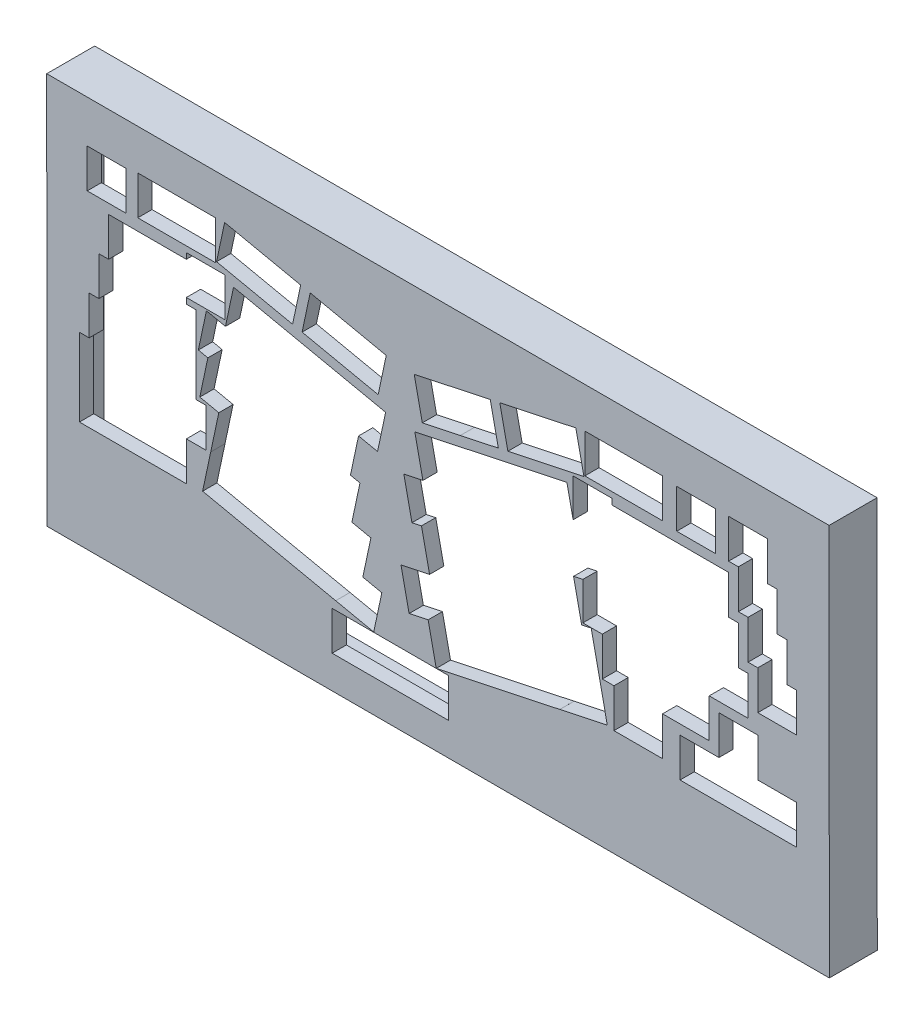
SolidWorks part; units mm, degrees
ref_plane "Front Plane" through (0, 0, 0) normal (0, 0, 1) x (1, 0, 0)
ref_plane "Top Plane" through (0, 0, 0) normal (0, 1, 0) x (1, 0, 0)
ref_plane "Right Plane" through (0, 0, 0) normal (1, 0, 0) x (0, 0, -1)
sketch "Model" plane through (0, 0, 0) normal (0, 0, 1) x (1, 0, 0)
  line L0 (3.8158, 5.1291) -> (3.565, 5.0023) construction
  line L1 (3.565, 5.0023) -> (3.3652, 4.8038) construction
  line L2 (3.3652, 4.8038) -> (3.2384, 4.5531) construction
  line L3 (3.2384, 4.5531) -> (3.1943, 4.2733) construction
  line L4 (3.1943, 4.2733) -> (3.2384, 3.9949) construction
  line L5 (3.2384, 3.9949) -> (3.3652, 3.7441) construction
  line L6 (3.3652, 3.7441) -> (3.565, 3.5457) construction
  line L7 (3.565, 3.5457) -> (3.8158, 3.4189) construction
  line L8 (3.8158, 3.4189) -> (4.0942, 3.3734) construction
  line L9 (4.0942, 3.3734) -> (4.3725, 3.4189) construction
  line L10 (4.3725, 3.4189) -> (4.6233, 3.5457) construction
  line L11 (4.6233, 3.5457) -> (4.8231, 3.7441) construction
  line L12 (4.8231, 3.7441) -> (4.9499, 3.9949) construction
  line L13 (4.9499, 3.9949) -> (4.994, 4.2733) construction
  line L14 (4.994, 4.2733) -> (4.9499, 4.5531) construction
  line L15 (4.9499, 4.5531) -> (4.8231, 4.8038) construction
  line L16 (4.8231, 4.8038) -> (4.6233, 5.0023) construction
  line L17 (4.6233, 5.0023) -> (4.3725, 5.1291) construction
  line L18 (4.3725, 5.1291) -> (4.0942, 5.1732) construction
  line L19 (4.0942, 5.1732) -> (3.8158, 5.1291) construction
  line L20 (75.7107, 5.1291) -> (75.4599, 5.0023) construction
  line L21 (75.4599, 5.0023) -> (75.2602, 4.8038) construction
  line L22 (75.2602, 4.8038) -> (75.1321, 4.5531) construction
  line L23 (75.1321, 4.5531) -> (75.088, 4.2733) construction
  line L24 (75.088, 4.2733) -> (75.1321, 3.9949) construction
  line L25 (75.1321, 3.9949) -> (75.2602, 3.7441) construction
  line L26 (75.2602, 3.7441) -> (75.4599, 3.5457) construction
  line L27 (75.4599, 3.5457) -> (75.7107, 3.4189) construction
  line L28 (75.7107, 3.4189) -> (75.989, 3.3734) construction
  line L29 (75.989, 3.3734) -> (76.2663, 3.4189) construction
  line L30 (76.2663, 3.4189) -> (76.5168, 3.5457) construction
  line L31 (76.5168, 3.5457) -> (76.7168, 3.7441) construction
  line L32 (76.7168, 3.7441) -> (76.8449, 3.9949) construction
  line L33 (76.8449, 3.9949) -> (76.889, 4.2733) construction
  line L34 (76.889, 4.2733) -> (76.8449, 4.5531) construction
  line L35 (76.8449, 4.5531) -> (76.7168, 4.8038) construction
  line L36 (76.7168, 4.8038) -> (76.5168, 5.0023) construction
  line L37 (76.5168, 5.0023) -> (76.2663, 5.1291) construction
  line L38 (76.2663, 5.1291) -> (75.989, 5.1732) construction
  line L39 (75.989, 5.1732) -> (75.7107, 5.1291) construction
  line L40 (147.606, 5.1291) -> (147.355, 5.0023) construction
  line L41 (147.355, 5.0023) -> (147.155, 4.8038) construction
  line L42 (147.155, 4.8038) -> (147.027, 4.5531) construction
  line L43 (147.027, 4.5531) -> (146.983, 4.2733) construction
  line L44 (146.983, 4.2733) -> (147.027, 3.9949) construction
  line L45 (147.027, 3.9949) -> (147.155, 3.7441) construction
  line L46 (147.155, 3.7441) -> (147.355, 3.5457) construction
  line L47 (147.355, 3.5457) -> (147.606, 3.4189) construction
  line L48 (147.606, 3.4189) -> (147.884, 3.3734) construction
  line L49 (147.884, 3.3734) -> (148.161, 3.4189) construction
  line L50 (148.161, 3.4189) -> (148.412, 3.5457) construction
  line L51 (148.412, 3.5457) -> (148.612, 3.7441) construction
  line L52 (148.612, 3.7441) -> (148.74, 3.9949) construction
  line L53 (148.74, 3.9949) -> (148.784, 4.2733) construction
  line L54 (148.784, 4.2733) -> (148.74, 4.5531) construction
  line L55 (148.74, 4.5531) -> (148.612, 4.8038) construction
  line L56 (148.612, 4.8038) -> (148.412, 5.0023) construction
  line L57 (148.412, 5.0023) -> (148.161, 5.1291) construction
  line L58 (148.161, 5.1291) -> (147.884, 5.1732) construction
  line L59 (147.884, 5.1732) -> (147.606, 5.1291) construction
  line L60 (219.499, 5.1291) -> (219.25, 5.0023) construction
  line L61 (219.25, 5.0023) -> (219.049, 4.8038) construction
  line L62 (219.049, 4.8038) -> (218.922, 4.5531) construction
  line L63 (218.922, 4.5531) -> (218.878, 4.2733) construction
  line L64 (218.878, 4.2733) -> (218.922, 3.9949) construction
  line L65 (218.922, 3.9949) -> (219.049, 3.7441) construction
  line L66 (219.049, 3.7441) -> (219.25, 3.5457) construction
  line L67 (219.25, 3.5457) -> (219.499, 3.4189) construction
  line L68 (219.499, 3.4189) -> (219.778, 3.3734) construction
  line L69 (219.778, 3.3734) -> (220.056, 3.4189) construction
  line L70 (220.056, 3.4189) -> (220.307, 3.5457) construction
  line L71 (220.307, 3.5457) -> (220.507, 3.7441) construction
  line L72 (220.507, 3.7441) -> (220.635, 3.9949) construction
  line L73 (220.635, 3.9949) -> (220.679, 4.2733) construction
  line L74 (220.679, 4.2733) -> (220.635, 4.5531) construction
  line L75 (220.635, 4.5531) -> (220.507, 4.8038) construction
  line L76 (220.507, 4.8038) -> (220.307, 5.0023) construction
  line L77 (220.307, 5.0023) -> (220.056, 5.1291) construction
  line L78 (220.056, 5.1291) -> (219.778, 5.1732) construction
  line L79 (219.778, 5.1732) -> (219.499, 5.1291) construction
  line L80 (291.394, 5.1291) -> (291.144, 5.0023) construction
  line L81 (291.144, 5.0023) -> (290.944, 4.8038) construction
  line L82 (290.944, 4.8038) -> (290.817, 4.5531) construction
  line L83 (290.817, 4.5531) -> (290.773, 4.2733) construction
  line L84 (290.773, 4.2733) -> (290.817, 3.9949) construction
  line L85 (290.817, 3.9949) -> (290.944, 3.7441) construction
  line L86 (290.944, 3.7441) -> (291.144, 3.5457) construction
  line L87 (291.144, 3.5457) -> (291.394, 3.4189) construction
  line L88 (291.394, 3.4189) -> (291.673, 3.3734) construction
  line L89 (291.673, 3.3734) -> (291.95, 3.4189) construction
  line L90 (291.95, 3.4189) -> (292.202, 3.5457) construction
  line L91 (292.202, 3.5457) -> (292.401, 3.7441) construction
  line L92 (292.401, 3.7441) -> (292.529, 3.9949) construction
  line L93 (292.529, 3.9949) -> (292.573, 4.2733) construction
  line L94 (292.573, 4.2733) -> (292.529, 4.5531) construction
  line L95 (292.529, 4.5531) -> (292.401, 4.8038) construction
  line L96 (292.401, 4.8038) -> (292.202, 5.0023) construction
  line L97 (292.202, 5.0023) -> (291.95, 5.1291) construction
  line L98 (291.95, 5.1291) -> (291.673, 5.1732) construction
  line L99 (291.673, 5.1732) -> (291.394, 5.1291) construction
  line L100 (363.291, 5.1291) -> (363.04, 5.0023) construction
  line L101 (363.04, 5.0023) -> (362.839, 4.8038) construction
  line L102 (362.839, 4.8038) -> (362.712, 4.5531) construction
  line L103 (362.712, 4.5531) -> (362.67, 4.2733) construction
  line L104 (362.67, 4.2733) -> (362.712, 3.9949) construction
  line L105 (362.712, 3.9949) -> (362.839, 3.7441) construction
  line L106 (362.839, 3.7441) -> (363.04, 3.5457) construction
  line L107 (363.04, 3.5457) -> (363.291, 3.4189) construction
  line L108 (363.291, 3.4189) -> (363.569, 3.3734) construction
  line L109 (363.569, 3.3734) -> (363.844, 3.4189) construction
  line L110 (363.844, 3.4189) -> (364.098, 3.5457) construction
  line L111 (364.098, 3.5457) -> (364.296, 3.7441) construction
  line L112 (364.296, 3.7441) -> (364.423, 3.9949) construction
  line L113 (364.423, 3.9949) -> (364.469, 4.2733) construction
  line L114 (364.469, 4.2733) -> (364.423, 4.5531) construction
  line L115 (364.423, 4.5531) -> (364.296, 4.8038) construction
  line L116 (364.296, 4.8038) -> (364.098, 5.0023) construction
  line L117 (364.098, 5.0023) -> (363.844, 5.1291) construction
  line L118 (363.844, 5.1291) -> (363.569, 5.1732) construction
  line L119 (363.569, 5.1732) -> (363.291, 5.1291) construction
  line L120 (131.917, 27.3251) -> (189.071, 27.3251)
  line L121 (189.071, 27.3251) -> (189.071, 8.2737)
  line L122 (189.071, 8.2737) -> (131.917, 8.2737)
  line L123 (131.917, 8.2737) -> (131.917, 27.3251)
  line L124 (250.028, 142.579) -> (250.028, 123.963)
  line L125 (250.028, 123.963) -> (246.976, 138.322)
  line L126 (246.976, 138.322) -> (228.342, 134.36)
  line L127 (228.342, 134.36) -> (228.342, 134.361)
  line L128 (228.342, 134.361) -> (209.708, 130.4)
  line L129 (209.708, 130.4) -> (209.708, 130.401)
  line L130 (209.708, 130.401) -> (172.44, 122.479)
  line L131 (172.44, 122.479) -> (176.4, 103.845)
  line L132 (176.4, 103.845) -> (167.083, 101.865)
  line L133 (167.083, 101.865) -> (171.045, 83.228)
  line L134 (171.045, 83.228) -> (175.703, 84.2186)
  line L135 (175.703, 84.2186) -> (179.663, 65.5863)
  line L136 (179.663, 65.5863) -> (165.687, 62.6166)
  line L137 (165.687, 62.6166) -> (169.649, 43.9801)
  line L138 (169.649, 43.9801) -> (178.966, 45.9617)
  line L139 (178.966, 45.9617) -> (182.926, 27.3279)
  line L140 (182.926, 27.3279) -> (243.487, 40.2001)
  line L141 (243.487, 40.2001) -> (243.487, 40.1987)
  line L142 (243.487, 40.1987) -> (266.78, 45.1513)
  line L143 (266.78, 45.1513) -> (258.859, 82.4205)
  line L144 (258.859, 82.4205) -> (254.2, 81.431)
  line L145 (254.2, 81.431) -> (250.241, 100.062)
  line L146 (250.241, 100.062) -> (254.791, 101.03)
  line L147 (254.791, 101.03) -> (254.791, 82.568)
  line L148 (254.791, 82.568) -> (264.316, 82.568)
  line L149 (264.316, 82.568) -> (264.316, 63.518)
  line L150 (264.316, 63.518) -> (270.031, 63.518)
  line L151 (270.031, 63.518) -> (270.031, 44.468)
  line L152 (270.031, 44.468) -> (293.846, 44.468)
  line L153 (293.846, 44.468) -> (293.846, 63.518)
  line L154 (293.846, 63.518) -> (316.705, 63.518)
  line L155 (316.705, 63.518) -> (316.705, 82.568)
  line L156 (316.705, 82.568) -> (335.755, 82.568)
  line L157 (335.755, 82.568) -> (335.755, 101.621)
  line L158 (335.755, 101.621) -> (330.992, 101.621)
  line L159 (330.992, 101.621) -> (330.992, 120.671)
  line L160 (330.992, 120.671) -> (326.23, 120.671)
  line L161 (326.23, 120.671) -> (326.23, 139.721)
  line L162 (326.23, 139.721) -> (269.08, 139.721)
  line L163 (269.08, 139.721) -> (269.08, 142.579)
  line L164 (269.08, 142.579) -> (250.028, 142.579)
  line L165 (79.6452, 120.831) -> (70.327, 122.811)
  line L166 (70.327, 122.811) -> (66.3663, 104.176)
  line L167 (66.3663, 104.176) -> (71.0255, 103.185)
  line L168 (71.0255, 103.185) -> (67.0648, 84.551)
  line L169 (67.0648, 84.551) -> (76.382, 82.5722)
  line L170 (76.382, 82.5722) -> (72.42, 63.9367)
  line L171 (72.42, 63.9367) -> (72.4214, 63.9367)
  line L172 (72.4214, 63.9367) -> (68.4597, 45.303)
  line L173 (68.4597, 45.303) -> (133.679, 31.4399)
  line L174 (133.679, 31.4399) -> (133.679, 31.4413)
  line L175 (133.679, 31.4413) -> (152.313, 27.4808)
  line L176 (152.313, 27.4808) -> (156.275, 46.1162)
  line L177 (156.275, 46.1162) -> (146.958, 48.0949)
  line L178 (146.958, 48.0949) -> (150.919, 66.7286)
  line L179 (150.919, 66.7286) -> (141.602, 68.7091)
  line L180 (141.602, 68.7091) -> (145.562, 87.3428)
  line L181 (145.562, 87.3428) -> (140.903, 88.3338)
  line L182 (140.903, 88.3338) -> (144.865, 106.966)
  line L183 (144.865, 106.966) -> (154.182, 104.986)
  line L184 (154.182, 104.986) -> (158.142, 123.621)
  line L185 (158.142, 123.621) -> (139.507, 127.583)
  line L186 (139.507, 127.583) -> (139.507, 127.581)
  line L187 (139.507, 127.581) -> (83.6055, 139.464)
  line L188 (83.6055, 139.464) -> (79.6452, 120.831)
  line L189 (321.466, 77.8083) -> (321.466, 58.7583)
  line L190 (321.466, 58.7583) -> (302.416, 58.7583)
  line L191 (302.416, 58.7583) -> (302.416, 39.7069)
  line L192 (302.416, 39.7069) -> (359.569, 39.7069)
  line L193 (359.569, 39.7069) -> (359.569, 58.7583)
  line L194 (359.569, 58.7583) -> (340.517, 58.7583)
  line L195 (340.517, 58.7583) -> (340.517, 77.8083)
  line L196 (340.517, 77.8083) -> (321.466, 77.8083)
  line L197 (60.4795, 142.579) -> (60.4795, 139.721)
  line L198 (60.4795, 139.721) -> (22.3807, 139.721)
  line L199 (22.3807, 139.721) -> (22.3807, 120.671)
  line L200 (22.3807, 120.671) -> (17.6182, 120.671)
  line L201 (17.6182, 120.671) -> (17.6182, 101.621)
  line L202 (17.6182, 101.621) -> (12.8557, 101.621)
  line L203 (12.8557, 101.621) -> (12.8557, 82.5708)
  line L204 (12.8557, 82.5708) -> (8.0932, 82.5708)
  line L205 (8.0932, 82.5708) -> (8.0932, 44.468)
  line L206 (8.0932, 44.468) -> (60.482, 44.468)
  line L207 (60.482, 44.468) -> (60.482, 63.518)
  line L208 (60.482, 63.518) -> (70.007, 63.518)
  line L209 (70.007, 63.518) -> (70.007, 82.5708)
  line L210 (70.007, 82.5708) -> (65.2459, 82.5708)
  line L211 (65.2459, 82.5708) -> (65.2459, 120.671)
  line L212 (65.2459, 120.671) -> (60.482, 120.671)
  line L213 (60.482, 120.671) -> (60.482, 123.526)
  line L214 (60.482, 123.526) -> (79.532, 123.526)
  line L215 (79.532, 123.526) -> (79.532, 142.579)
  line L216 (79.532, 142.579) -> (60.4795, 142.579)
  line L217 (326.227, 163.533) -> (326.227, 144.482)
  line L218 (326.227, 144.482) -> (330.991, 144.482)
  line L219 (330.991, 144.482) -> (330.991, 125.432)
  line L220 (330.991, 125.432) -> (335.753, 125.432)
  line L221 (335.753, 125.432) -> (335.753, 106.382)
  line L222 (335.753, 106.382) -> (340.516, 106.382)
  line L223 (340.516, 106.382) -> (340.516, 87.3319)
  line L224 (340.516, 87.3319) -> (359.569, 87.3319)
  line L225 (359.569, 87.3319) -> (359.569, 106.383)
  line L226 (359.569, 106.383) -> (354.806, 106.383)
  line L227 (354.806, 106.383) -> (354.806, 125.433)
  line L228 (354.806, 125.433) -> (350.042, 125.433)
  line L229 (350.042, 125.433) -> (350.042, 144.483)
  line L230 (350.042, 144.483) -> (345.28, 144.483)
  line L231 (345.28, 144.483) -> (345.28, 163.533)
  line L232 (345.28, 163.533) -> (326.227, 163.533)
  line L233 (3.8158, 89.1399) -> (3.565, 89.0129) construction
  line L234 (3.565, 89.0129) -> (3.3652, 88.8132) construction
  line L235 (3.3652, 88.8132) -> (3.2384, 88.5624) construction
  line L236 (3.2384, 88.5624) -> (3.1943, 88.284) construction
  line L237 (3.1943, 88.284) -> (3.2384, 88.0071) construction
  line L238 (3.2384, 88.0071) -> (3.3652, 87.7549) construction
  line L239 (3.3652, 87.7549) -> (3.565, 87.5563) construction
  line L240 (3.565, 87.5563) -> (3.8158, 87.4282) construction
  line L241 (3.8158, 87.4282) -> (4.0942, 87.3841) construction
  line L242 (4.0942, 87.3841) -> (4.3725, 87.4282) construction
  line L243 (4.3725, 87.4282) -> (4.6233, 87.5563) construction
  line L244 (4.6233, 87.5563) -> (4.8231, 87.7549) construction
  line L245 (4.8231, 87.7549) -> (4.9499, 88.0071) construction
  line L246 (4.9499, 88.0071) -> (4.994, 88.284) construction
  line L247 (4.994, 88.284) -> (4.9499, 88.5624) construction
  line L248 (4.9499, 88.5624) -> (4.8231, 88.8132) construction
  line L249 (4.8231, 88.8132) -> (4.6233, 89.0129) construction
  line L250 (4.6233, 89.0129) -> (4.3725, 89.1399) construction
  line L251 (4.3725, 89.1399) -> (4.0942, 89.184) construction
  line L252 (4.0942, 89.184) -> (3.8158, 89.1399) construction
  line L253 (363.291, 89.1399) -> (363.04, 89.0129) construction
  line L254 (363.04, 89.0129) -> (362.839, 88.8132) construction
  line L255 (362.839, 88.8132) -> (362.712, 88.5624) construction
  line L256 (362.712, 88.5624) -> (362.67, 88.284) construction
  line L257 (362.67, 88.284) -> (362.712, 88.0071) construction
  line L258 (362.712, 88.0071) -> (362.839, 87.7549) construction
  line L259 (362.839, 87.7549) -> (363.04, 87.5563) construction
  line L260 (363.04, 87.5563) -> (363.291, 87.4282) construction
  line L261 (363.291, 87.4282) -> (363.569, 87.3841) construction
  line L262 (363.569, 87.3841) -> (363.844, 87.4282) construction
  line L263 (363.844, 87.4282) -> (364.098, 87.5563) construction
  line L264 (364.098, 87.5563) -> (364.296, 87.7549) construction
  line L265 (364.296, 87.7549) -> (364.423, 88.0071) construction
  line L266 (364.423, 88.0071) -> (364.469, 88.284) construction
  line L267 (364.469, 88.284) -> (364.423, 88.5624) construction
  line L268 (364.423, 88.5624) -> (364.296, 88.8132) construction
  line L269 (364.296, 88.8132) -> (364.098, 89.0129) construction
  line L270 (364.098, 89.0129) -> (363.844, 89.1399) construction
  line L271 (363.844, 89.1399) -> (363.569, 89.184) construction
  line L272 (363.569, 89.184) -> (363.291, 89.1399) construction
  line L273 (269.078, 120.671) -> (264.316, 120.671)
  line L274 (264.316, 120.671) -> (264.316, 101.621)
  line L275 (264.316, 101.621) -> (257.572, 101.621)
  line L276 (257.572, 101.621) -> (264.214, 103.032)
  line L277 (264.214, 103.032) -> (260.254, 121.668)
  line L278 (260.254, 121.668) -> (250.938, 119.688)
  line L279 (250.938, 119.688) -> (250.121, 123.526)
  line L280 (250.121, 123.526) -> (269.078, 123.526)
  line L281 (269.078, 123.526) -> (269.078, 120.671)
  line L282 (172.146, 146.761) -> (176.109, 128.126)
  line L283 (176.109, 128.126) -> (194.741, 132.086)
  line L284 (194.741, 132.086) -> (194.741, 132.085)
  line L285 (194.741, 132.085) -> (213.377, 136.047)
  line L286 (213.377, 136.047) -> (209.416, 154.682)
  line L287 (209.416, 154.682) -> (172.146, 146.761)
  line L288 (117.205, 137.189) -> (154.474, 129.267)
  line L289 (154.474, 129.267) -> (158.434, 147.903)
  line L290 (158.434, 147.903) -> (121.165, 155.826)
  line L291 (121.165, 155.826) -> (117.205, 137.189)
  line L292 (214.073, 155.673) -> (218.033, 137.036)
  line L293 (218.033, 137.036) -> (255.304, 144.959)
  line L294 (255.304, 144.959) -> (251.343, 163.594)
  line L295 (251.343, 163.594) -> (214.073, 155.673)
  line L296 (75.2782, 146.101) -> (112.547, 138.18)
  line L297 (112.547, 138.18) -> (116.509, 156.815)
  line L298 (116.509, 156.815) -> (97.874, 160.776)
  line L299 (97.874, 160.776) -> (79.2399, 164.736)
  line L300 (79.2399, 164.736) -> (75.2782, 146.101)
  line L301 (300.797, 163.533) -> (319.848, 163.533)
  line L302 (319.848, 163.533) -> (319.848, 144.482)
  line L303 (319.848, 144.482) -> (300.797, 144.482)
  line L304 (300.797, 144.482) -> (300.797, 163.533)
  line L305 (11.9035, 163.533) -> (30.9549, 163.533)
  line L306 (30.9549, 163.533) -> (30.9549, 144.482)
  line L307 (30.9549, 144.482) -> (11.9035, 144.482)
  line L308 (11.9035, 144.482) -> (11.9035, 163.533)
  line L309 (255.743, 164.485) -> (293.846, 164.485)
  line L310 (293.846, 164.485) -> (293.846, 145.434)
  line L311 (293.846, 145.434) -> (255.743, 145.434)
  line L312 (255.743, 145.434) -> (255.743, 164.485)
  line L313 (36.6681, 164.485) -> (74.7709, 164.485)
  line L314 (74.7709, 164.485) -> (74.7709, 145.434)
  line L315 (74.7709, 145.434) -> (36.6681, 145.434)
  line L316 (36.6681, 145.434) -> (36.6681, 164.485)
  line L317 (3.8158, 173.15) -> (3.565, 173.024) construction
  line L318 (3.565, 173.024) -> (3.3652, 172.824) construction
  line L319 (3.3652, 172.824) -> (3.2384, 172.573) construction
  line L320 (3.2384, 172.573) -> (3.1943, 172.295) construction
  line L321 (3.1943, 172.295) -> (3.2384, 172.016) construction
  line L322 (3.2384, 172.016) -> (3.3652, 171.766) construction
  line L323 (3.3652, 171.766) -> (3.565, 171.566) construction
  line L324 (3.565, 171.566) -> (3.8158, 171.439) construction
  line L325 (3.8158, 171.439) -> (4.0942, 171.395) construction
  line L326 (4.0942, 171.395) -> (4.3725, 171.439) construction
  line L327 (4.3725, 171.439) -> (4.6233, 171.566) construction
  line L328 (4.6233, 171.566) -> (4.8231, 171.766) construction
  line L329 (4.8231, 171.766) -> (4.9499, 172.016) construction
  line L330 (4.9499, 172.016) -> (4.994, 172.295) construction
  line L331 (4.994, 172.295) -> (4.9499, 172.573) construction
  line L332 (4.9499, 172.573) -> (4.8231, 172.824) construction
  line L333 (4.8231, 172.824) -> (4.6233, 173.024) construction
  line L334 (4.6233, 173.024) -> (4.3725, 173.15) construction
  line L335 (4.3725, 173.15) -> (4.0942, 173.194) construction
  line L336 (4.0942, 173.194) -> (3.8158, 173.15) construction
  line L337 (363.291, 173.15) -> (363.04, 173.024) construction
  line L338 (363.04, 173.024) -> (362.839, 172.824) construction
  line L339 (362.839, 172.824) -> (362.712, 172.573) construction
  line L340 (362.712, 172.573) -> (362.67, 172.295) construction
  line L341 (362.67, 172.295) -> (362.712, 172.016) construction
  line L342 (362.712, 172.016) -> (362.839, 171.766) construction
  line L343 (362.839, 171.766) -> (363.04, 171.566) construction
  line L344 (363.04, 171.566) -> (363.291, 171.439) construction
  line L345 (363.291, 171.439) -> (363.569, 171.395) construction
  line L346 (363.569, 171.395) -> (363.844, 171.439) construction
  line L347 (363.844, 171.439) -> (364.098, 171.566) construction
  line L348 (364.098, 171.566) -> (364.296, 171.766) construction
  line L349 (364.296, 171.766) -> (364.423, 172.016) construction
  line L350 (364.423, 172.016) -> (364.469, 172.295) construction
  line L351 (364.469, 172.295) -> (364.423, 172.573) construction
  line L352 (364.423, 172.573) -> (364.296, 172.824) construction
  line L353 (364.296, 172.824) -> (364.098, 173.024) construction
  line L354 (364.098, 173.024) -> (363.844, 173.15) construction
  line L355 (363.844, 173.15) -> (363.569, 173.194) construction
  line L356 (363.569, 173.194) -> (363.291, 173.15) construction
  line L357 (291.394, 173.15) -> (291.144, 173.024) construction
  line L358 (291.144, 173.024) -> (290.944, 172.824) construction
  line L359 (290.944, 172.824) -> (290.817, 172.573) construction
  line L360 (290.817, 172.573) -> (290.773, 172.295) construction
  line L361 (290.773, 172.295) -> (290.817, 172.016) construction
  line L362 (290.817, 172.016) -> (290.944, 171.766) construction
  line L363 (290.944, 171.766) -> (291.144, 171.566) construction
  line L364 (291.144, 171.566) -> (291.394, 171.439) construction
  line L365 (291.394, 171.439) -> (291.673, 171.395) construction
  line L366 (291.673, 171.395) -> (291.95, 171.439) construction
  line L367 (291.95, 171.439) -> (292.202, 171.566) construction
  line L368 (292.202, 171.566) -> (292.401, 171.766) construction
  line L369 (292.401, 171.766) -> (292.529, 172.016) construction
  line L370 (292.529, 172.016) -> (292.573, 172.295) construction
  line L371 (292.573, 172.295) -> (292.529, 172.573) construction
  line L372 (292.529, 172.573) -> (292.401, 172.824) construction
  line L373 (292.401, 172.824) -> (292.202, 173.024) construction
  line L374 (292.202, 173.024) -> (291.95, 173.15) construction
  line L375 (291.95, 173.15) -> (291.673, 173.194) construction
  line L376 (291.673, 173.194) -> (291.394, 173.15) construction
  line L377 (219.499, 173.15) -> (219.25, 173.024) construction
  line L378 (219.25, 173.024) -> (219.049, 172.824) construction
  line L379 (219.049, 172.824) -> (218.922, 172.573) construction
  line L380 (218.922, 172.573) -> (218.878, 172.295) construction
  line L381 (218.878, 172.295) -> (218.922, 172.016) construction
  line L382 (218.922, 172.016) -> (219.049, 171.766) construction
  line L383 (219.049, 171.766) -> (219.25, 171.566) construction
  line L384 (219.25, 171.566) -> (219.499, 171.439) construction
  line L385 (219.499, 171.439) -> (219.778, 171.395) construction
  line L386 (219.778, 171.395) -> (220.056, 171.439) construction
  line L387 (220.056, 171.439) -> (220.307, 171.566) construction
  line L388 (220.307, 171.566) -> (220.507, 171.766) construction
  line L389 (220.507, 171.766) -> (220.635, 172.016) construction
  line L390 (220.635, 172.016) -> (220.679, 172.295) construction
  line L391 (220.679, 172.295) -> (220.635, 172.573) construction
  line L392 (220.635, 172.573) -> (220.507, 172.824) construction
  line L393 (220.507, 172.824) -> (220.307, 173.024) construction
  line L394 (220.307, 173.024) -> (220.056, 173.15) construction
  line L395 (220.056, 173.15) -> (219.778, 173.194) construction
  line L396 (219.778, 173.194) -> (219.499, 173.15) construction
  line L397 (147.606, 173.15) -> (147.355, 173.024) construction
  line L398 (147.355, 173.024) -> (147.155, 172.824) construction
  line L399 (147.155, 172.824) -> (147.027, 172.573) construction
  line L400 (147.027, 172.573) -> (146.983, 172.295) construction
  line L401 (146.983, 172.295) -> (147.027, 172.016) construction
  line L402 (147.027, 172.016) -> (147.155, 171.766) construction
  line L403 (147.155, 171.766) -> (147.355, 171.566) construction
  line L404 (147.355, 171.566) -> (147.606, 171.439) construction
  line L405 (147.606, 171.439) -> (147.884, 171.395) construction
  line L406 (147.884, 171.395) -> (148.161, 171.439) construction
  line L407 (148.161, 171.439) -> (148.412, 171.566) construction
  line L408 (148.412, 171.566) -> (148.612, 171.766) construction
  line L409 (148.612, 171.766) -> (148.74, 172.016) construction
  line L410 (148.74, 172.016) -> (148.784, 172.295) construction
  line L411 (148.784, 172.295) -> (148.74, 172.573) construction
  line L412 (148.74, 172.573) -> (148.612, 172.824) construction
  line L413 (148.612, 172.824) -> (148.412, 173.024) construction
  line L414 (148.412, 173.024) -> (148.161, 173.15) construction
  line L415 (148.161, 173.15) -> (147.884, 173.194) construction
  line L416 (147.884, 173.194) -> (147.606, 173.15) construction
  line L417 (75.7107, 173.15) -> (75.4599, 173.024) construction
  line L418 (75.4599, 173.024) -> (75.2602, 172.824) construction
  line L419 (75.2602, 172.824) -> (75.1321, 172.573) construction
  line L420 (75.1321, 172.573) -> (75.088, 172.295) construction
  line L421 (75.088, 172.295) -> (75.1321, 172.016) construction
  line L422 (75.1321, 172.016) -> (75.2602, 171.766) construction
  line L423 (75.2602, 171.766) -> (75.4599, 171.566) construction
  line L424 (75.4599, 171.566) -> (75.7107, 171.439) construction
  line L425 (75.7107, 171.439) -> (75.989, 171.395) construction
  line L426 (75.989, 171.395) -> (76.2663, 171.439) construction
  line L427 (76.2663, 171.439) -> (76.5168, 171.566) construction
  line L428 (76.5168, 171.566) -> (76.7168, 171.766) construction
  line L429 (76.7168, 171.766) -> (76.8449, 172.016) construction
  line L430 (76.8449, 172.016) -> (76.889, 172.295) construction
  line L431 (76.889, 172.295) -> (76.8449, 172.573) construction
  line L432 (76.8449, 172.573) -> (76.7168, 172.824) construction
  line L433 (76.7168, 172.824) -> (76.5168, 173.024) construction
  line L434 (76.5168, 173.024) -> (76.2663, 173.15) construction
  line L435 (76.2663, 173.15) -> (75.989, 173.194) construction
  line L436 (75.989, 173.194) -> (75.7107, 173.15) construction
  line L437 (-7.9049, -7.7268) -> (-7.9354, 184.294)
  line L438 (-7.9354, 184.294) -> (375.4737, 184.294)
  line L439 (375.4737, 184.294) -> (375.566, -7.7437)
  line L440 (375.566, -7.7437) -> (-7.9049, -7.7268)
  line L441 (-0.4014, 176.794) -> (368.0633, 176.794)
  line L442 (-0.4101, -0.2271) -> (-0.4014, 176.794)
  line L443 (368.066, -0.2208) -> (-0.4101, -0.2271)
  line L444 (368.0633, 176.794) -> (368.066, -0.2208)
  point P445 (0, 0)
extrude "凸台-拉伸1" add sketch "Model" along normal blind 23.5 contours L444 L441 L442 L443 L436 L435 L434 L433 L432 L431 L430 L429 L428 L427 L426 L425 L424 L423 L422 L421 L420 L419 L418 L417 L416 L415 L414 L413 L412 L411 L410 L409 L408 L407 L406 L405 L404 L403 L402 L401 L400 L399 L398 L397 L396 L395 L394 L393 | L440 L439 L438 L437 L441 L444 L443 L442
sketch "草图2" plane through (0, 0, 0) normal (0, 0, -1) x (-1, 0, 0)
  line L0 (-368.0633, 176.794) -> (0.4101, -0.2271) construction
  line L2 (0.4134, -0.2266) -> (-368.0666, -0.2266)
  line L3 (0.4134, -0.2266) -> (0.4134, 176.7934)
  line L4 (0.4134, 176.7934) -> (-368.0666, 176.7934)
  line L5 (-368.0666, -0.2266) -> (-368.0666, 176.7934)
  line L6 (0.4134, -0.2266) -> (-368.0666, 176.7934) construction
  line L7 (0.4134, 176.7934) -> (-368.0666, -0.2266) construction
  point P4 (-183.8266, 88.2834)
  dimension "D1" = 368.48
  dimension "D2" = 177.02
extrude "切除-拉伸1" cut sketch "草图2" against normal blind 16.5
sketch "草图3" plane through (0, 0, 0) normal (0, 0, -1) x (-1, 0, 0)
  line L8 (-374.0653, -6.2436) -> (6.4052, -6.2269)
  line L9 (6.4052, -6.2269) -> (6.4351, 182.794)
  line L10 (6.4351, 182.794) -> (-373.9744, 182.794)
  line L11 (-373.9744, 182.794) -> (-374.0653, -6.2436)
  line L12 (-374.0653, -6.2436) -> (6.4052, -6.2269)
  line L13 (6.4052, -6.2269) -> (6.4351, 182.794)
  line L14 (6.4351, 182.794) -> (-373.9744, 182.794)
  line L15 (-373.9744, 182.794) -> (-374.0653, -6.2436)
  dimension "D1" = 1.5
extrude "切除-拉伸2" cut sketch "草图3" against normal blind 3
